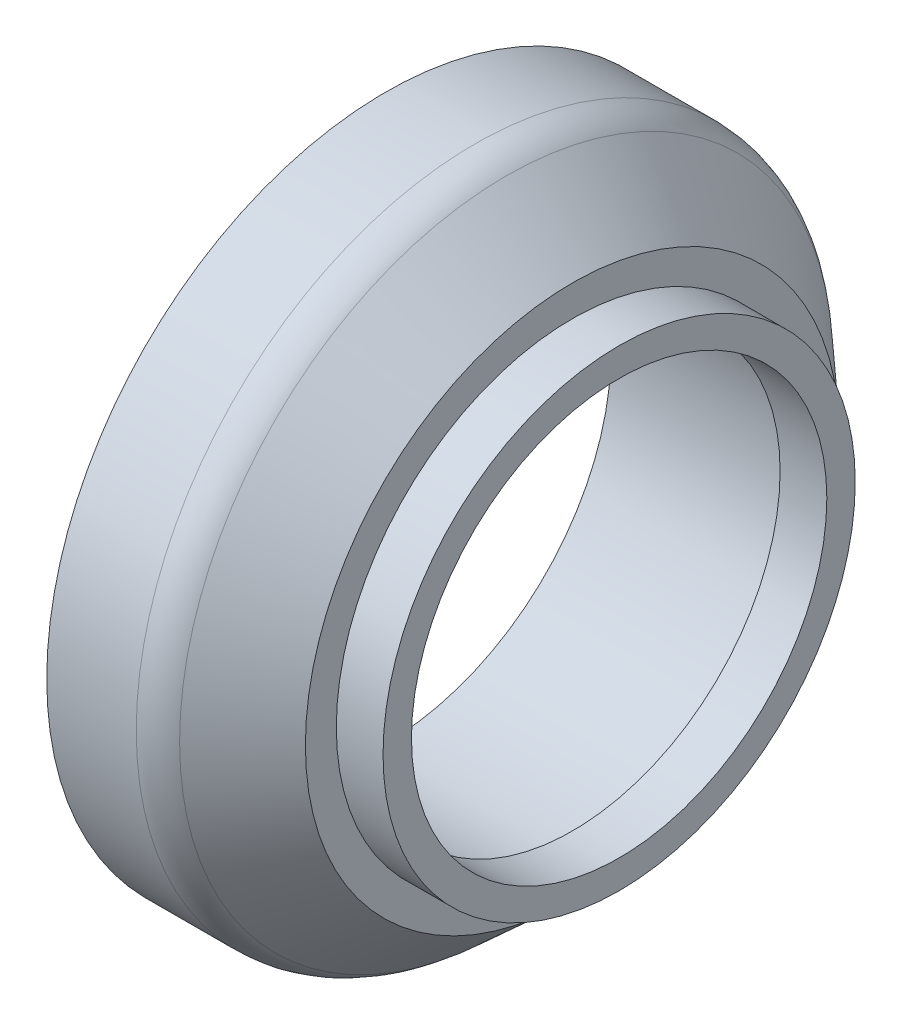
SolidWorks part; units mm, degrees
ref_plane "Front Plane" through (0, 0, 0) normal (0, 0, 1) x (1, 0, 0)
ref_plane "Top Plane" through (0, 0, 0) normal (0, 1, 0) x (1, 0, 0)
ref_plane "Right Plane" through (0, 0, 0) normal (1, 0, 0) x (0, 0, -1)
sketch "Sketch1" plane through (0, 0, 0) normal (0, 0, 1) x (1, 0, 0)
  line L0 (0, 48.25) -> (0, 0) construction
  line L1 (0, 0) -> (36.8024, 0) construction
  line L2 (0, 48.25) -> (40, 48.25)
  line L3 (40, 48.25) -> (40, 57.15)
  line L4 (40, 57.15) -> (23, 72.5)
  line L5 (23, 72.5) -> (0, 72.5)
  line L6 (0, 72.5) -> (0, 48.25)
  dimension "D1" = 40
  dimension "D2" = 57.15
  dimension "D3" = 72.5
  dimension "D4" = 48.25
  dimension "D5" = 23
revolve "Revolve1" add sketch "Sketch1" angle 360 about L1
fillet "Fillet1" radius 10 1 edges at (23, 0, 72.5)
sketch "Sketch2" plane through (40, 0, 0) normal (1, 0, 0) x (0, 0, -1)
  circle A0 centre (0, 0) radius 50.53
  circle A1 centre (0, 0) radius 44.45
  dimension "D1" = 101.06
  dimension "D2" = 88.9
extrude "Boss-Extrude1" add sketch "Sketch2" along normal blind 10
sketch "Sketch3" plane through (0, 0, 0) normal (-1, 0, 0) x (0, 0, 1)
  circle A0 centre (0, 0) radius 62.5 construction
  circle A1 centre (-1.7184, 62.4764) radius 5.35
  dimension "D1" = 125
  dimension "D2" = 10.7
extrude "Cut-Extrude1" cut sketch "Sketch3" against normal blind 19.4
chamfer "Chamfer1" distance 1 angle 45 1 edges at (0, 62.4764, 3.6316)
pattern_circular "CirPattern1" count 12 over 360 about axis through (0, 0, 0) along (1, 0, 0) of "Chamfer1", "Cut-Extrude1"
